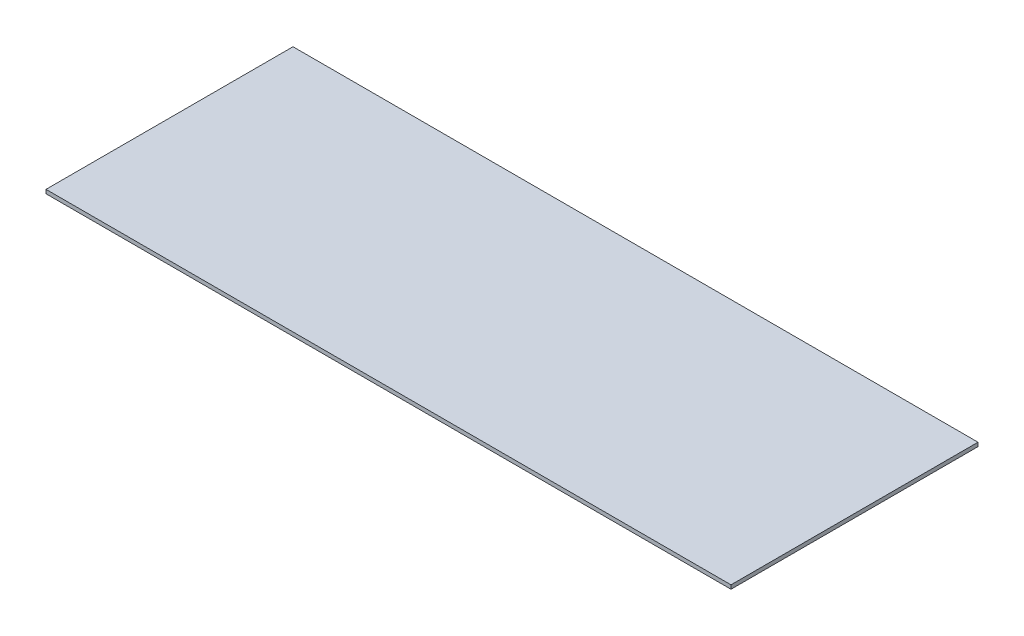
SolidWorks part; units mm, degrees
ref_plane "Front Plane" through (0, 0, 0) normal (0, 0, 1) x (1, 0, 0)
ref_plane "Top Plane" through (0, 0, 0) normal (0, 1, 0) x (1, 0, 0)
ref_plane "Right Plane" through (0, 0, 0) normal (1, 0, 0) x (0, 0, -1)
sketch "Sketch1" plane through (0, 0, 0) normal (0, 1, 0) x (1, 0, 0)
  line L1 (-22.185, 8) -> (22.185, 8)
  line L2 (-22.185, 8) -> (-22.185, -8)
  line L3 (-22.185, -8) -> (22.185, -8)
  line L4 (22.185, 8) -> (22.185, -8)
  line L5 (-22.185, 8) -> (22.185, -8) construction
  line L6 (-22.185, -8) -> (22.185, 8) construction
  point P0 (0, 0)
  dimension "D1" = 44.37
  dimension "D2" = 16
extrude "Boss-Extrude1" add sketch "Sketch1" along normal blind 0.25
